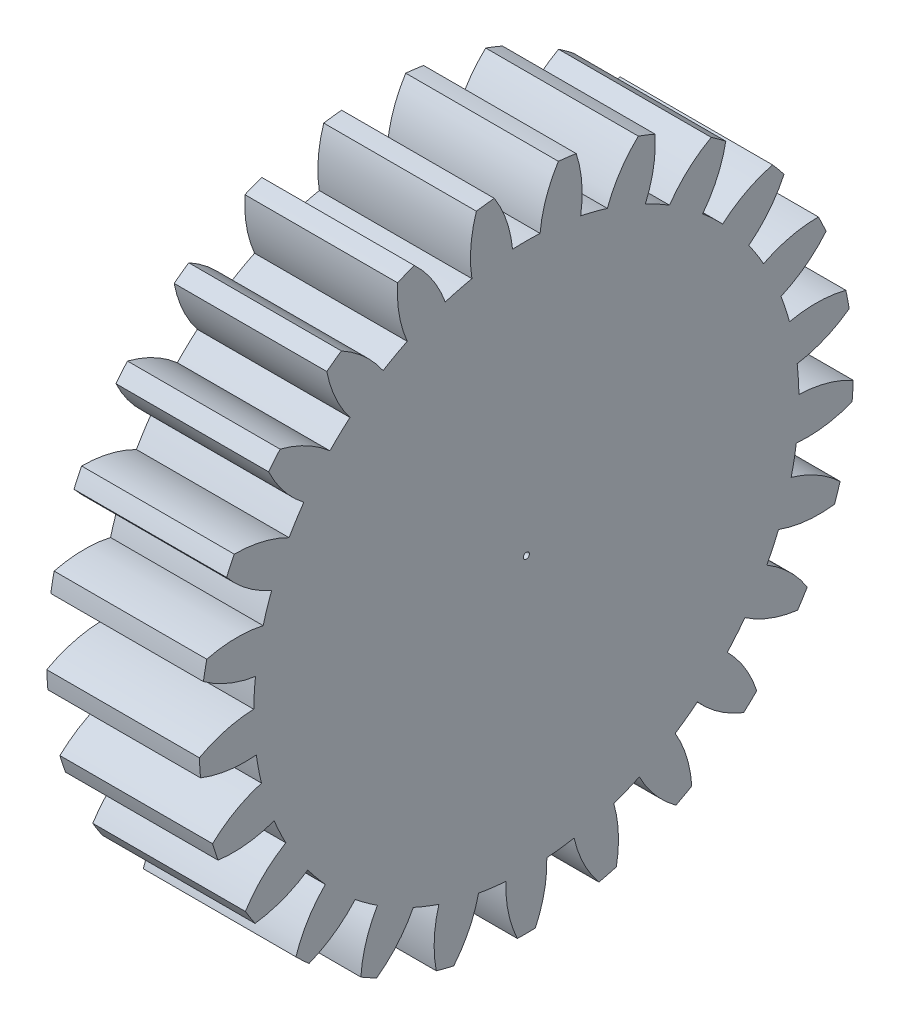
SolidWorks part; units mm, degrees
ref_plane "Plane1" through (0, 0, 0) normal (0, 0, 1) x (1, 0, 0)
ref_plane "Plane2" through (0, 0, 0) normal (0, 1, 0) x (1, 0, 0)
ref_plane "Plane3" through (0, 0, 0) normal (1, 0, 0) x (0, 0, -1)
sketch "HoldingSke" plane through (0, 0, 0) normal (0, 1, 0) x (1, 0, 0)
  line L0 (0, 0) -> (184.1617, -85.876)
  line L1 (-15, 0) -> (100, 0) construction
  line L2 (0, 0) -> (-2.1039, 2.3779)
  line L3 (0, 0) -> (-11.863, 4.5341)
  line L4 (0, 0) -> (7.8269, 3.6497)
  line L5 (0, 0) -> (-47.5972, -17.7524)
  line L6 (0, 0) -> (-16.5793, -11.1861)
  line L7 (-2.1039, 2.3779) -> (8.8308, 51.9871)
  line L8 (-76.2, 54.61) -> (-75.184, 54.61)
  line L9 (-67.7845, 28.3722) -> (-49.3413, 33.142)
  line L10 (-76.2, 71.12) -> (104.1128, 71.12)
  line L11 (0, 0) -> (-20, 0)
  line L12 (-76.2, 101.6) -> (-76.0857, 101.6)
  line L13 (24.9733, 27.94) -> (52.9518, 28.4284)
  line L14 (24.9733, 27.94) -> (24.9746, 27.94)
  line L15 (24.9733, 27.94) -> (100.4006, 29.5858)
  circle A0 centre (0, 0) radius 0.3969
  circle A1 centre (0, 0) radius 35.7175
  circle A2 centre (0, 0) radius 38.1
  circle A3 centre (0, 0) radius 0.3969
  dimension "MHD" = 71.435
  dimension "Hub_dia" = 76.2
  dimension "Bore" = 0.7937
  dimension "MBD" = 0.7937
  dimension "Num_teeth" = 25
  dimension "Pitch" = 203.2
  dimension "Overall_len" = 50.8
  dimension "Show_teeth" = 25
  dimension "Thickness" = 20
  dimension "OAL" = 50.8001
  dimension "T_dim" = 1.016
  dimension "Ap" = 14.5
  dimension "H" = 19.05
  dimension "Pitch_radius" = 180.3128
  dimension "Width" = 20
  dimension "Backlash" = 0.1143
  dimension "Addendum_fac" = 1
  dimension "Dedendum_fac" = 1.25
  dimension "Clearance_fac" = 0.25
  dimension "Dedendum_add" = 0.0013
sketch "BasProSke" plane through (0, 0, 0) normal (0, 1, 0) x (1, 0, 0)
  line L0 (-10, 0) -> (60, 0) construction
  line L1 (0, 0) -> (0, 42.8625)
  line L2 (0, 0) -> (20, 0)
  line L3 (20, 0) -> (20, 42.8625)
  line L4 (20, 42.8625) -> (0, 42.8625)
  dimension "Thickness" = 20
  dimension "Diameter" = 85.725
revolve "Base-Revolve" add sketch "BasProSke" angle 360 about L0
sketch "TooCutSke" plane through (0, 0, 0) normal (1, 0, 0) x (0, 0, -1)
  line L1 (0, 0) -> (0, 107) construction
  line L2 (0, 0) -> (-2.692, 39.5961) construction
  line L3 (0, 0) -> (-9.9317, 78.6177) construction
  line L4 (-2.692, 39.5961) -> (-4.9659, 39.3088) construction
  arc A0 (1.8025, 35.672) -> (-1.8025, 35.672) centre (0, 0) ccw
  arc A1 (4.2143, 42.6803) -> (-4.2143, 42.6803) centre (0, 0) ccw
  circle A2 centre (0, 0) radius 39.6875 construction
  circle A3 centre (0, 0) radius 38.4234 construction
  arc A4 (-1.8025, 35.672) -> (-4.2143, 42.6803) centre (-17.6047, 34.153) ccw
  arc A5 (4.2143, 42.6803) -> (1.8025, 35.672) centre (17.6047, 34.153) ccw
  dimension "Root_dia" = 71.435
  dimension "Overcut_dia" = 85.7758
  dimension "Pitch_dia" = 79.375
  dimension "Base_dia" = 76.8467
  dimension "Flank_rad" = 15.875
  dimension "Half_ang" = 7.2
  dimension "Half_CT" = 2.292
extrude "ToothCut" cut sketch "TooCutSke" along normal through all
fillet "Breaks" [suppressed] radius 0.0635
fillet "RootFillets" [suppressed] radius 0.795
pattern_circular "TeethCuts" count 25 every 14.4 about axis through (-10, 0, 0) along (1, 0, 0) of "ToothCut", "RootFillets", "Breaks"
sketch "HubNeaOneSke" plane through (0, 0, 0) normal (-1, 0, 0) x (0, 0, 1)
  circle A0 centre (0, 0) radius 35.7175
  dimension "Diameter" = 71.435
extrude "HubNearOne" [suppressed] add sketch "HubNeaOneSke" along normal blind 30.8001
sketch "HubNeaBotSke" plane through (0, 0, 0) normal (-1, 0, 0) x (0, 0, 1)
  circle A0 centre (0, 0) radius 35.7175
  dimension "Diameter" = 71.435
extrude "HubNearBoth" [suppressed] add sketch "HubNeaBotSke" along normal blind 15.4
ref_plane "FarPln" through (20, 0, 0) normal (1, 0, 0) x (0, 0, -1)
sketch "HubFarSke" plane through (20, 0, 0) normal (1, 0, 0) x (0, 0, -1)
  circle A0 centre (0, 0) radius 35.7175
  dimension "Diameter" = 71.435
extrude "HubFar" [suppressed] add sketch "HubFarSke" along normal blind 15.4
sketch "BorSke" plane through (0, 0, 0) normal (1, 0, 0) x (0, 0, -1)
  circle A0 centre (0, 0) radius 0.3969
  dimension "Diameter" = 0.7937
extrude "Bore" cut sketch "BorSke" along normal mid plane 101.6001
sketch "KeySke" plane through (0, 0, 0) normal (1, 0, 0) x (0, 0, -1)
  line L0 (-0.127, 0) -> (-0.127, 0.6191)
  line L1 (-0.127, 0.6191) -> (0.127, 0.6191)
  line L2 (0.127, 0.6191) -> (0.127, 0)
  line L3 (0, 0) -> (0, 34) construction
  line L4 (-0.127, 0) -> (0.127, 0)
  dimension "Offset" = 0.6191
  dimension "Width" = 0.254
extrude "Keyway" [suppressed] cut sketch "KeySke" along normal mid plane 101.6001
pattern_circular "Keyway2" [suppressed] count 2 every 90 about axis through (-10, 0, 0) along (1, 0, 0)
equation "' \"Pitch@HoldingSke\" = 4"
equation "' \"Num_teeth@HoldingSke\" = 12"
equation "' \"Ap@HoldingSke\" =  20"
equation "' \"Ap@HoldingSke\" = 20"
equation "' \"Width@HoldingSke\" = 0.5"
equation "' \"Hub_dia@HoldingSke\"= 1"
equation "' \"Hub_dia@HoldingSke\" = 1"
equation "' \"Overall_len@HoldingSke\" = 1.0"
equation "' \"Bore@HoldingSke\" = 0.75"
equation "' \"T_dim@HoldingSke\" = 0.85"
equation "' \"Width@KeySke\" = 0.25"
equation "' \"Show_teeth@HoldingSke\" = 13"
equation "' \"Backlash@HoldingSke\" = 0.009"
equation "' \"Addendum_fac@HoldingSke\" = 1.0"
equation "' \"Dedendum_fac@HoldingSke\" = 1.25"
equation "' \"Dedendum_add@HoldingSke\" = 0.00005"
equation "' \"Clearance_fac@HoldingSke\" = 0.25"
equation "' \"Pitch@HoldingSke\" = 0.5"
equation "' \"Num_teeth@HoldingSke\" = 23"
equation "' \"Show_teeth@HoldingSke\" = 23"
equation "' \"Backlash@HoldingSke\" = 0.0375"
equation "\"Overcut_dia@TooCutSke\" = (\"Num_teeth@HoldingSke\" + 2 * \"Addendum_fac@HoldingSke\") / \"Pitch@HoldingSke\" + 0.002"
equation "\"Pitch_dia@TooCutSke\" = \"Num_teeth@HoldingSke\" / \"Pitch@HoldingSke\""
equation "\"Base_dia@TooCutSke\" = \"Num_teeth@HoldingSke\" / \"Pitch@HoldingSke\" * cos((\"Ap@HoldingSke\"  * 3.14159265 / 180))"
equation "\"Root_dia@TooCutSke\" = (\"Num_teeth@HoldingSke\" + 2) / \"Pitch@HoldingSke\" - 2 * (\"Addendum_fac@HoldingSke\" + \"Dedendum_fac@HoldingSke\") / \"Pitch@HoldingSke\" - \"Dedendum_add@HoldingSke\" * 2"
equation "\"Half_ang@TooCutSke\" = 180 / \"Num_teeth@HoldingSke\""
equation "\"Half_CT@TooCutSke\" = \"Num_teeth@HoldingSke\" / \"Pitch@HoldingSke\" * sin((3.14159265 / 2 / \"Num_teeth@HoldingSke\")) / 2 - 7 * \"Backlash@HoldingSke\" / 4"
equation "\"Flank_rad@TooCutSke\" = \"Num_teeth@HoldingSke\" / \"Pitch@HoldingSke\" / 5"
equation "\"Radius@RootFillets\" = \"Clearance_fac@HoldingSke\" / \"Pitch@HoldingSke\" + \"Dedendum_add@HoldingSke\""
equation "\"Break_rad@Breaks\" = 0.02 / \"Pitch@HoldingSke\""
equation "\"Thickness@HoldingSke\" = \"Width@HoldingSke\""
equation "\"OAL@HoldingSke\" = \"Thickness@HoldingSke\""
equation "\"MHD@HoldingSke\" = (\"Num_teeth@HoldingSke\" + 2) / \"Pitch@HoldingSke\" - 2 * (\"Addendum_fac@HoldingSke\" + \"Dedendum_fac@HoldingSke\")  / \"Pitch@HoldingSke\" - \"Dedendum_add@HoldingSke\" * 2"
equation "\"MBD@HoldingSke\" = (\"Num_teeth@HoldingSke\" + 2) / \"Pitch@HoldingSke\" - 2 * (\"Addendum_fac@HoldingSke\" + \"Dedendum_fac@HoldingSke\")  / \"Pitch@HoldingSke\" - \"Dedendum_add@HoldingSke\" * 2 - 0.002"
equation "\"MHD@HoldingSke\" = ((sgn( \"MHD@HoldingSke\" - \"Hub_dia@HoldingSke\" )-1)*( \"MHD@HoldingSke\" - \"Hub_dia@HoldingSke\" ))/-2+ \"Hub_dia@HoldingSke\""
equation "\"MBD@HoldingSke\" = ((sgn( \"MBD@HoldingSke\" - \"Bore@HoldingSke\" )-1)*( \"MBD@HoldingSke\" - \"Bore@HoldingSke\" ))/-2+ \"Bore@HoldingSke\""
equation "\"OAL@HoldingSke\" = ((sgn( \"OAL@HoldingSke\" - \"Overall_len@HoldingSke\" )+1)*( \"OAL@HoldingSke\" - \"Overall_len@HoldingSke\" ))/2 + \"Overall_len@HoldingSke\" + 0.000002"
equation "\"Num_teeth@TeethCuts\" = int( \"Show_teeth@HoldingSke\" ) + 1"
equation "\"Num_teeth@TeethCuts\" = ((sgn( \"Num_teeth@TeethCuts\" - \"Num_teeth@HoldingSke\" )-1)*( \"Num_teeth@TeethCuts\" - \"Num_teeth@HoldingSke\" ))/-2+ \"Num_teeth@HoldingSke\""
equation "\"Num_teeth@TeethCuts\" = ((sgn( \"Num_teeth@TeethCuts\" - 2.0)+1)*( \"Num_teeth@TeethCuts\" - 2.0))/2 +2.0"
equation "\"Angle@TeethCuts\" = 360.0 / \"Num_teeth@HoldingSke\""
equation "\"Diameter@BasProSke\" = (\"Num_teeth@HoldingSke\" + 2 * \"Addendum_fac@HoldingSke\") / \"Pitch@HoldingSke\""
equation "\"Thickness@BasProSke\"  = \"Thickness@HoldingSke\""
equation "' \"Fillet_rad@BasProSke\" =  \"Thickness@HoldingSke\" * 0.05"
equation "' \"Fillet_rad@BasProSke\" = \"Thickness@HoldingSke\" * 0.05"
equation "\"MHD@HoldingSke\" = ((sgn( \"MHD@HoldingSke\" - \"Root_dia@TooCutSke\" )-1)*( \"MHD@HoldingSke\" - \"Root_dia@TooCutSke\" ))/-2+ \"Root_dia@TooCutSke\""
equation "\"Diameter@HubNeaOneSke\" = \"MHD@HoldingSke\""
equation "\"Length@HubNearOne\" = \"OAL@HoldingSke\" - \"Thickness@BasProSke\""
equation "\"Diameter@HubNeaBotSke\" = \"MHD@HoldingSke\""
equation "\"Length@HubNearBoth\" = ( \"OAL@HoldingSke\" - \"Thickness@BasProSke\" ) / 2.0"
equation "\"Thickness@FarPln\" = \"Thickness@BasProSke\""
equation "\"Diameter@HubFarSke\" = \"MHD@HoldingSke\""
equation "\"Length@HubFar\" = ( \"OAL@HoldingSke\" - \"Thickness@BasProSke\" ) / 2.0"
equation "\"Diameter@BorSke\" = \"MBD@HoldingSke\""
equation "\"D1@Bore\" = \"OAL@HoldingSke\" * 2.0"
equation "\"D1@Keyway\" = \"OAL@HoldingSke\" * 2.0"
equation "\"Offset@KeySke\" = \"T_dim@HoldingSke\" - \"MBD@HoldingSke\" / 2.0"
